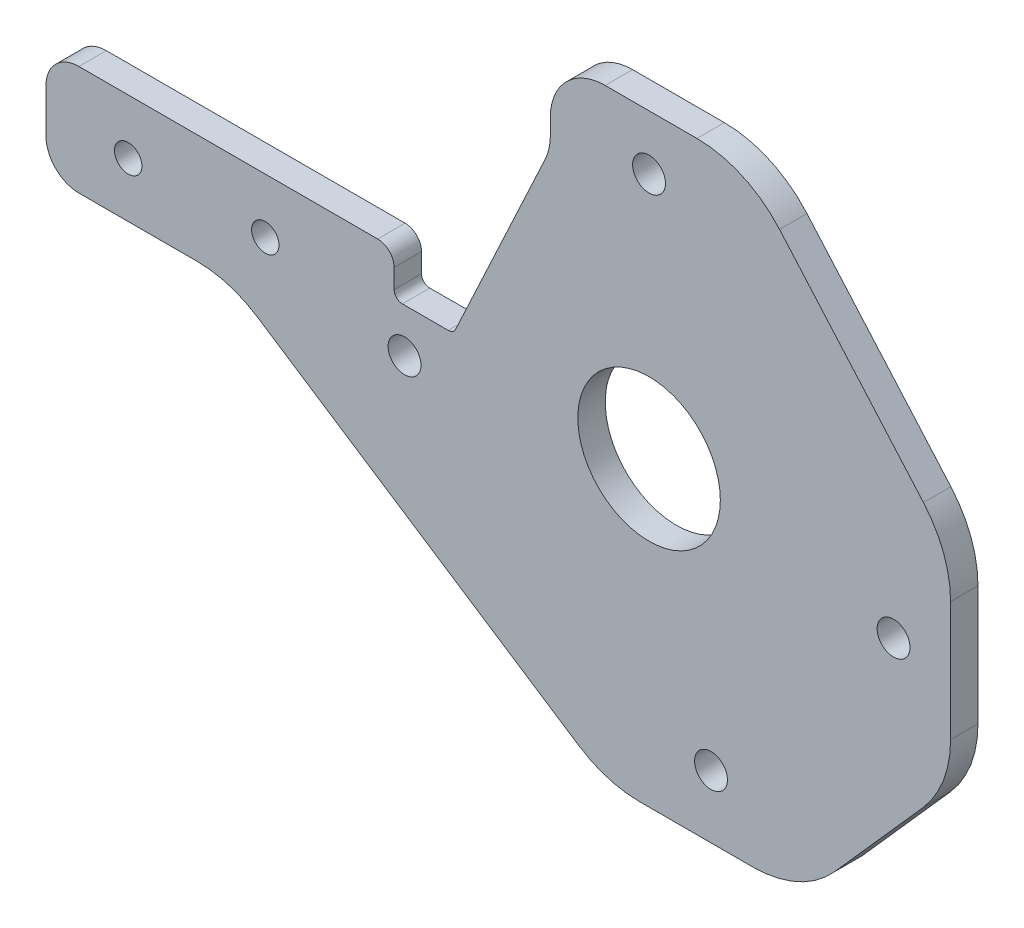
SolidWorks part; units mm, degrees
ref_plane "Front Plane" through (0, 0, 0) normal (0, 0, 1) x (1, 0, 0)
ref_plane "Top Plane" through (0, 0, 0) normal (0, 1, 0) x (1, 0, 0)
ref_plane "Right Plane" through (0, 0, 0) normal (1, 0, 0) x (0, 0, -1)
sketch "Sketch1" plane through (0, 0, 0) normal (0, 0, 1) x (1, 0, 0)
  line L0 (-55, 10) -> (-110, 10)
  line L1 (-55, -55) -> (55, -55)
  line L2 (-55, -55) -> (-55, -10)
  line L3 (-55, 55) -> (55, 55)
  line L4 (55, -55) -> (55, 55)
  line L5 (-55, -55) -> (55, 55) construction
  line L6 (-55, 55) -> (55, -55) construction
  line L7 (-110, 10) -> (-110, -10)
  line L12 (-110, -10) -> (-55, -10)
  line L13 (-55, 10) -> (-55, 55)
  line L14 (0, 0) -> (-55, 0) construction
  line L15 (-55, 10) -> (-55, -10) construction
  line L16 (-55, 0) -> (-110, 0) construction
  circle A0 centre (0, 45) radius 3
  circle A1 centre (-44.5982, -6) radius 3
  circle A2 centre (44.5982, -6) radius 3
  circle A3 centre (11.3, -43.5581) radius 3
  circle A4 centre (0, 0) radius 13
  circle A7 centre (-95, 0) radius 2.5
  circle A8 centre (-70, 0) radius 2.5
  point P0 (11.3, -43.5581)
  point P1 (44.5982, -6)
  point P2 (0, 45)
  point P3 (-44.5982, -6)
  point P13 (0, 0)
  dimension "D13" = 26
  dimension "D16" = 55
  dimension "D14" = 5
  dimension "D2" = 6
  dimension "D3" = 25
  dimension "D12" = 110
  dimension "D15" = 20
  dimension "D17" = 15
extrude "Boss-Extrude1" add sketch "Sketch1" along normal mid plane 5
sketch "Sketch2" plane through (0, 0, 0) normal (0, 0, 1) x (1, 0, 0)
  line L0 (-44.8704, -6.7953) -> (0, 45) construction
  line L1 (0, 45) -> (44.5982, -6) construction
  line L2 (44.5982, -6) -> (11.3, -43.5581) construction
  line L3 (11.3, -43.5581) -> (-44.8704, -6.7953) construction
  line L5 (-55, 10) -> (-55, 55) construction
  line L6 (-55, 55) -> (55, 55) construction
  line L7 (17.8237, 55) -> (55, 12.4873)
  line L8 (55, -55) -> (55, 55) construction
  line L9 (55, -24.4153) -> (27.8843, -55)
  line L10 (-55, -55) -> (55, -55) construction
  line L11 (-7.7391, -55) -> (-55, -24.0683)
  line L12 (-55, -55) -> (-55, -10) construction
  line L13 (-31.3696, -39.5342) -> (-20.4171, -22.7997) construction
  line L14 (41.4421, -39.7077) -> (26.4768, -26.4397) construction
  line L15 (36.4119, 33.7436) -> (21.3564, 20.578) construction
  line L17 (-55, -55) -> (-55, -24.0683)
  line L18 (-55, -55) -> (-7.7391, -55)
  line L19 (55, -55) -> (55, -24.4153)
  line L20 (-55, 55) -> (-18, 55)
  line L21 (-55, 10) -> (-55, 55)
  line L22 (17.8237, 55) -> (55, 55)
  line L23 (55, 12.4873) -> (55, 55)
  line L24 (27.8843, -55) -> (55, -55)
  line L26 (-18, 55) -> (-18, 39.9055)
  line L27 (-18, 39.9055) -> (-35.6756, 2)
  line L28 (-20, 39.9055) -> (-18, 39.9055) construction
  line L29 (-35.6756, 2) -> (-46.5, 2)
  line L31 (-55, 10) -> (-46.5, 10)
  line L32 (-46.5, 10) -> (-46.5, 2)
  dimension "D1" = 20
  dimension "D2" = 115
  dimension "D3" = 2
  dimension "D4" = 8.5
  dimension "D5" = 8
extrude "Cut-Extrude1" cut sketch "Sketch2" against normal through all both and the other way through all
sketch "Sketch3" plane through (0, 0, 0) normal (0, 0, 1) x (1, 0, 0)
  line L0 (-55, -24.0683) -> (-76.4952, -10)
  line L1 (-110, -10) -> (-55, -10) construction
  line L2 (-76.4952, -10) -> (-55, -10)
  line L3 (-55, -10) -> (-55, -24.0683)
  line L4 (-7.7391, -55) -> (-55, -24.0683) construction
extrude "Boss-Extrude2" add sketch "Sketch3" along normal up to surface and the other way up to surface up to face at (-24.7648, 0.5649, 2.5) other way up to face at (-24.7648, 0.5649, -2.5)
fillet "Fillet2" radius 20 6 edges at (-7.7391, -55, 0) (27.8843, -55, 0) (55, -24.4153, 0) (55, 12.4873, 0) (17.8237, 55, 0) (-76.4952, -10, 0)
fillet "Fillet4" radius 6 2 edges at (-110, 10, 0) (-110, -10, 0)
fillet "Fillet5" radius 10 2 edges at (-18, 39.9055, 0) (-18, 55, 0)
fillet "Fillet6" radius 3 1 edges at (-46.5, 10, 0)
fillet "Fillet7" radius 1.5 2 edges at (-35.6756, 2, 0) (-46.5, 2, 0)
